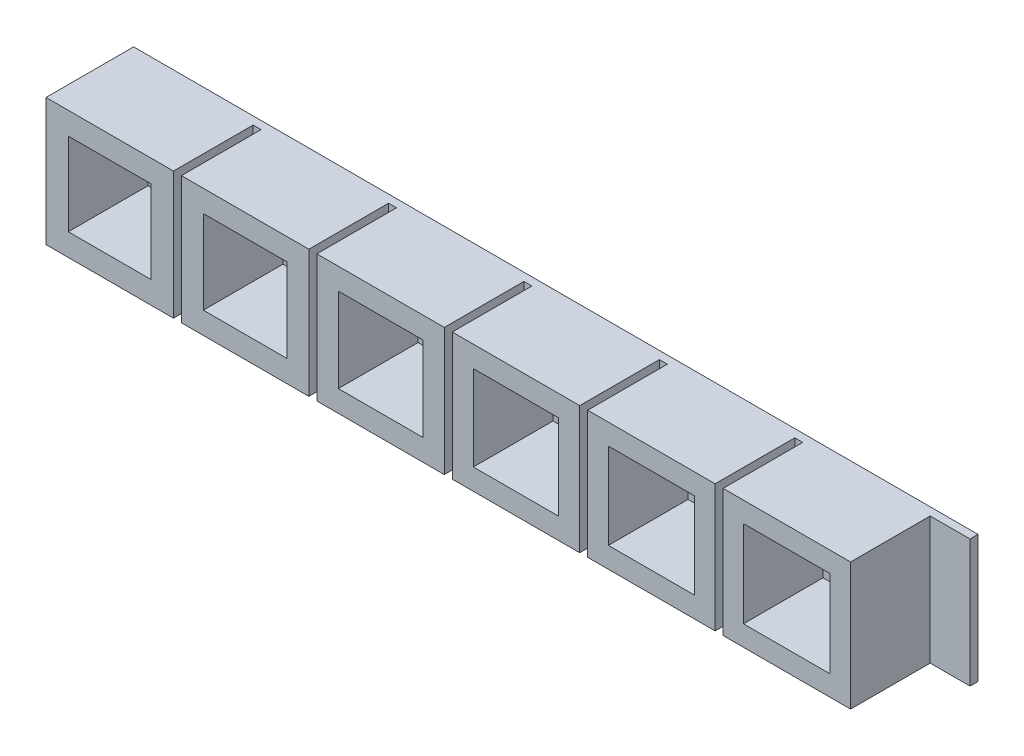
SolidWorks part; units mm, degrees
ref_plane "前视基准面" through (0, 0, 0) normal (0, 0, 1) x (1, 0, 0)
ref_plane "上视基准面" through (0, 0, 0) normal (0, 1, 0) x (1, 0, 0)
ref_plane "右视基准面" through (0, 0, 0) normal (1, 0, 0) x (0, 0, -1)
ref_plane "基准面4" through (0, 0, 0) normal (0, 0, -1) x (-1, 0, 0)
sketch "草图1" plane through (0, 0, 0) normal (0, 0, -1) x (-1, 0, 0)
  line L0 (0, -20) -> (-106, -20)
  line L1 (-106, -20) -> (-106, -36)
  line L2 (-106, -36) -> (0, -36)
  line L3 (0, -36) -> (0, -20)
extrude "凸台-拉伸1" add sketch "草图1" against normal blind 11
sketch "草图2" plane through (0, -20, 0) normal (0, 1, 0) x (-1, 0, 0)
  line L0 (-106, 1) -> (-101, 1)
  line L1 (-101, 1) -> (-101, 11)
  line L2 (-101, 11) -> (-106, 11)
  line L3 (-106, 11) -> (-106, 1)
extrude "切除-拉伸1" cut sketch "草图2" against normal through all
sketch "草图3" plane through (0, -20, 0) normal (0, 1, 0) x (-1, 0, 0)
  line L0 (-85, 11) -> (-85, 1)
  line L1 (-85, 1) -> (-84, 1)
  line L2 (-84, 1) -> (-84, 11)
  line L3 (-84, 11) -> (-85, 11)
extrude "切除-拉伸2" cut sketch "草图3" against normal through all
sketch "草图4" plane through (0, -20, 0) normal (0, 1, 0) x (-1, 0, 0)
  line L0 (-67, 11) -> (-68, 11)
  line L1 (-68, 11) -> (-68, 1)
  line L2 (-68, 1) -> (-67, 1)
  line L3 (-67, 1) -> (-67, 11)
extrude "切除-拉伸3" cut sketch "草图4" against normal through all
sketch "草图5" plane through (0, -20, 0) normal (0, 1, 0) x (-1, 0, 0)
  line L0 (-50, 11) -> (-51, 11)
  line L1 (-51, 11) -> (-51, 1)
  line L2 (-51, 1) -> (-50, 1)
  line L3 (-50, 1) -> (-50, 11)
extrude "切除-拉伸4" cut sketch "草图5" against normal through all
sketch "草图6" plane through (0, -20, 0) normal (0, 1, 0) x (-1, 0, 0)
  line L0 (-33, 11) -> (-34, 11)
  line L1 (-34, 11) -> (-34, 1)
  line L2 (-34, 1) -> (-33, 1)
  line L3 (-33, 1) -> (-33, 11)
extrude "切除-拉伸5" cut sketch "草图6" against normal through all
sketch "草图7" plane through (0, -20, 0) normal (0, 1, 0) x (-1, 0, 0)
  line L0 (-16, 11) -> (-17, 11)
  line L1 (-17, 11) -> (-17, 1)
  line L2 (-17, 1) -> (-16, 1)
  line L3 (-16, 1) -> (-16, 11)
extrude "切除-拉伸6" cut sketch "草图7" against normal through all
sketch "草图8" plane through (0, 0, 11) normal (0, 0, 1) x (1, 0, 0)
  line L0 (13.2, -33.2) -> (13.2, -22.8)
  line L1 (13.2, -22.8) -> (2.8, -22.8)
  line L2 (2.8, -22.8) -> (2.8, -33.2)
  line L3 (2.8, -33.2) -> (13.2, -33.2)
extrude "切除-拉伸7" cut sketch "草图8" against normal blind 10
sketch "草图9" plane through (0, 0, 11) normal (0, 0, 1) x (1, 0, 0)
  line L0 (30.25, -33.25) -> (30.25, -22.75)
  line L1 (30.25, -22.75) -> (19.75, -22.75)
  line L2 (19.75, -22.75) -> (19.75, -33.25)
  line L3 (19.75, -33.25) -> (30.25, -33.25)
extrude "切除-拉伸8" cut sketch "草图9" against normal blind 10
sketch "草图10" plane through (0, 0, 11) normal (0, 0, 1) x (1, 0, 0)
  line L0 (47.3, -33.3) -> (47.3, -22.7)
  line L1 (47.3, -22.7) -> (36.7, -22.7)
  line L2 (36.7, -22.7) -> (36.7, -33.3)
  line L3 (36.7, -33.3) -> (47.3, -33.3)
extrude "切除-拉伸9" cut sketch "草图10" against normal blind 10
sketch "草图11" plane through (0, 0, 11) normal (0, 0, 1) x (1, 0, 0)
  line L0 (64.35, -33.35) -> (64.35, -22.65)
  line L1 (64.35, -22.65) -> (53.65, -22.65)
  line L2 (53.65, -22.65) -> (53.65, -33.35)
  line L3 (53.65, -33.35) -> (64.35, -33.35)
extrude "切除-拉伸10" cut sketch "草图11" against normal blind 10
sketch "草图12" plane through (0, 0, 11) normal (0, 0, 1) x (1, 0, 0)
  line L0 (81.4, -33.4) -> (81.4, -22.6)
  line L1 (81.4, -22.6) -> (70.6, -22.6)
  line L2 (70.6, -22.6) -> (70.6, -33.4)
  line L3 (70.6, -33.4) -> (81.4, -33.4)
extrude "切除-拉伸11" cut sketch "草图12" against normal blind 10
sketch "草图13" plane through (0, 0, 11) normal (0, 0, 1) x (1, 0, 0)
  line L0 (98.45, -33.45) -> (98.45, -22.55)
  line L1 (98.45, -22.55) -> (87.55, -22.55)
  line L2 (87.55, -22.55) -> (87.55, -33.45)
  line L3 (87.55, -33.45) -> (98.45, -33.45)
extrude "切除-拉伸12" cut sketch "草图13" against normal blind 10
